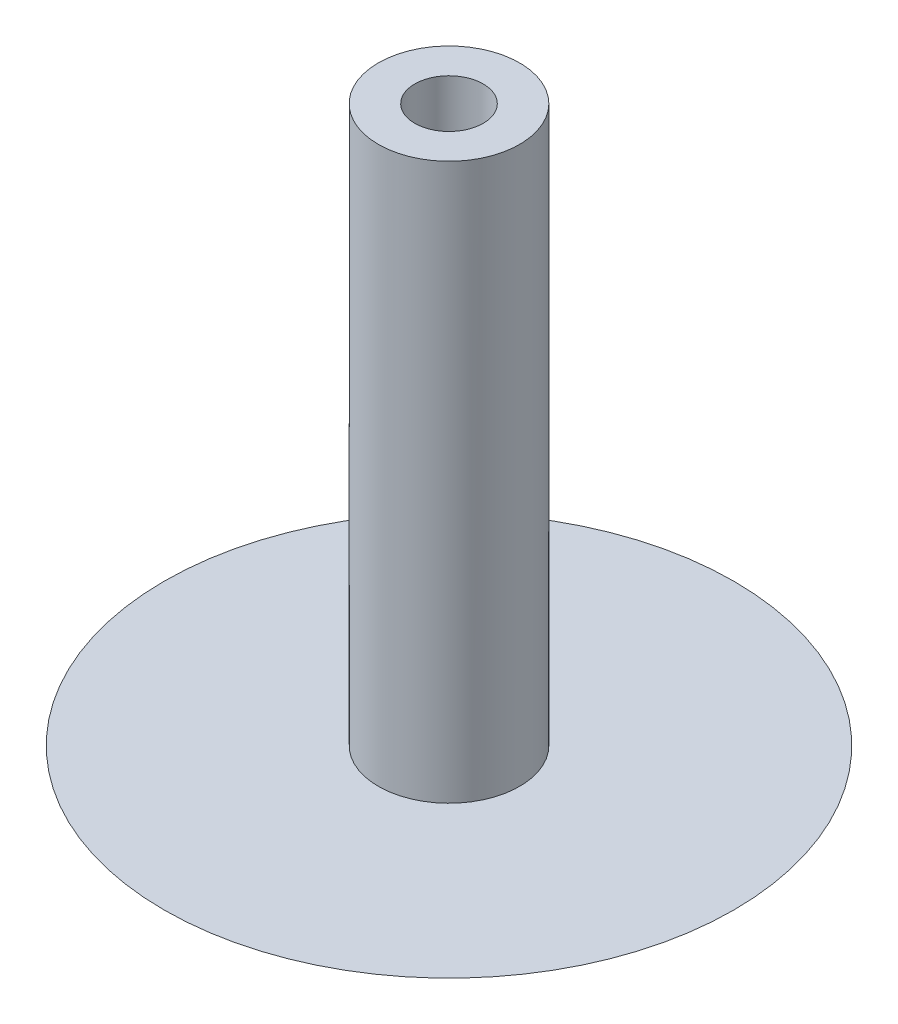
SolidWorks part; units mm, degrees
ref_plane "Front Plane" through (0, 0, 0) normal (0, 0, 1) x (1, 0, 0)
ref_plane "Top Plane" through (0, 0, 0) normal (0, 1, 0) x (1, 0, 0)
ref_plane "Right Plane" through (0, 0, 0) normal (1, 0, 0) x (0, 0, -1)
sketch "Sketch1" plane through (0, 0, 0) normal (0, 1, 0) x (1, 0, 0)
  circle A0 centre (0, 0) radius 1.9685
  circle A1 centre (0, 0) radius 0.9525
  dimension "D1" = 3.937
  dimension "D2" = 1.905
extrude "Boss-Extrude1" add sketch "Sketch1" along normal blind 15.494
sketch "Sketch2" plane through (0, 0, 0) normal (0, 0, 1) x (1, 0, 0)
  line L0 (-7.9375, 0) -> (7.9375, 0)
  line L1 (0, 0) -> (0, -2.54)
  arc A0 (7.9375, 0) -> (-7.9375, 0) centre (0, 11.1323) cw
  point P4 (0, 0)
  dimension "D1" = 15.875
  dimension "D2" = 2.54
revolve "Revolve1" add sketch "Sketch2" angle 360 about L1
